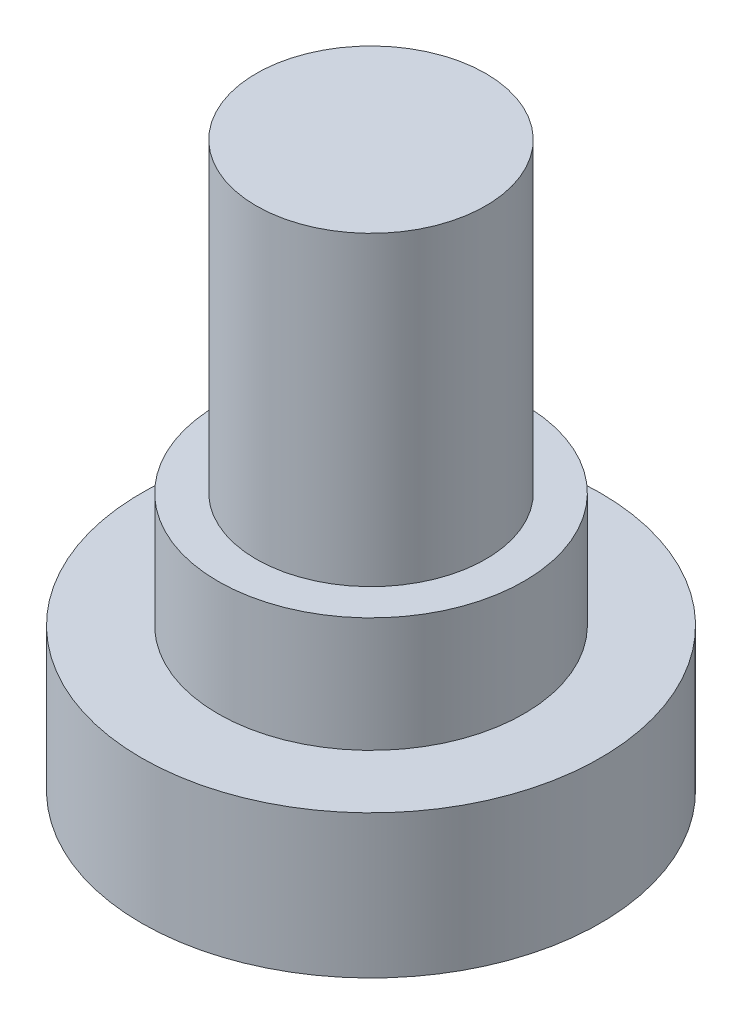
SolidWorks part; units mm, degrees
ref_plane "前视基准面" through (0, 0, 0) normal (0, 0, 1) x (1, 0, 0)
ref_plane "上视基准面" through (0, 0, 0) normal (0, 1, 0) x (1, 0, 0)
ref_plane "右视基准面" through (0, 0, 0) normal (1, 0, 0) x (0, 0, -1)
sketch "草图1" plane through (0, 0, 0) normal (0, 1, 0) x (1, 0, 0)
  circle A0 centre (0, 0) radius 6
extrude "凸台-拉伸1" add sketch "草图1" along normal blind 3.74
sketch "草图2" plane through (0, 3.74, 0) normal (0, 1, 0) x (1, 0, 0)
  circle A0 centre (0, 0) radius 4
extrude "凸台-拉伸2" add sketch "草图2" along normal blind 3
sketch "草图3" plane through (0, 6.74, 0) normal (0, 1, 0) x (1, 0, 0)
  circle A0 centre (0, 0) radius 3
extrude "凸台-拉伸3" add sketch "草图3" along normal blind 8
